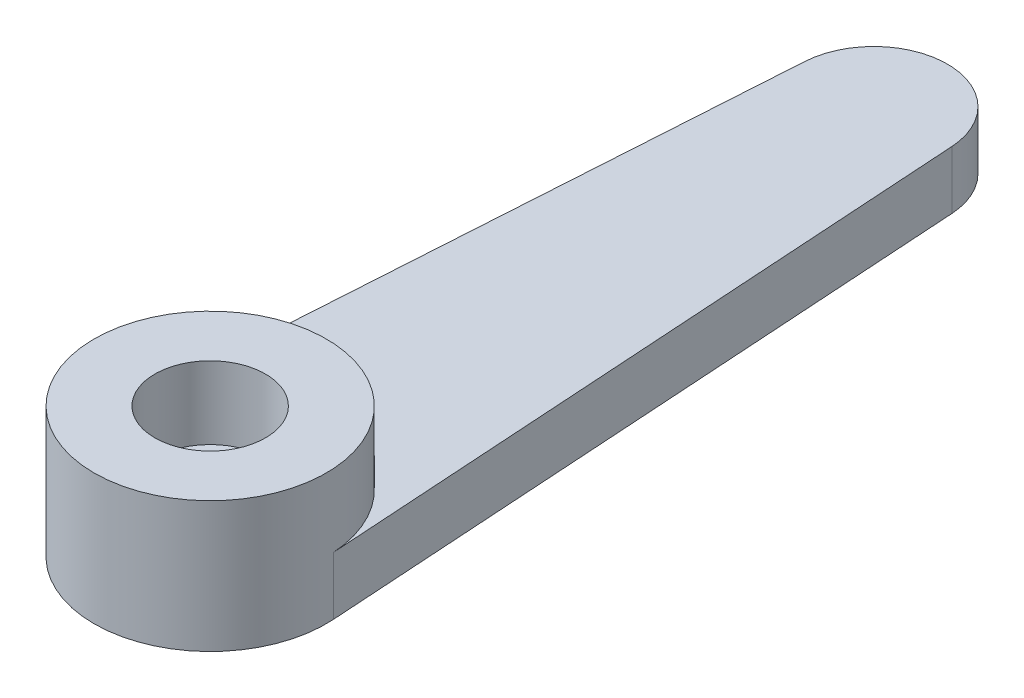
SolidWorks part; units mm, degrees
ref_plane "Front Plane" through (0, 0, 0) normal (0, 0, 1) x (1, 0, 0)
ref_plane "Top Plane" through (0, 0, 0) normal (0, 1, 0) x (1, 0, 0)
ref_plane "Right Plane" through (0, 0, 0) normal (1, 0, 0) x (0, 0, -1)
sketch "Sketch1" plane through (0, 0, 0) normal (0, 1, 0) x (1, 0, 0)
  line L0 (0, 0) -> (0, 25.4) construction
  line L1 (-2.5348, 23.0222) -> (-3.9918, 0.2555)
  line L2 (2.5348, 23.0222) -> (3.9918, 0.2555)
  circle A0 centre (0, 0) radius 4
  circle A1 centre (0, 22.86) radius 2.54
  dimension "D1" = 8
  dimension "D3" = 5.08
  dimension "D2" = 25.4
extrude "Boss-Extrude1" add sketch "Sketch1" along normal blind 2
sketch "Sketch2" plane through (0, 2, 0) normal (0, 1, 0) x (1, 0, 0)
  circle A0 centre (0, 0) radius 4
  circle A1 centre (0, 0) radius 1.9064
extrude "Boss-Extrude2" add sketch "Sketch2" along normal blind 2.5
sketch "Sketch3" plane through (0, 0, 0) normal (0, -1, 0) x (1, 0, 0)
  line L0 (0, 0) -> (0, -25.4) construction
  arc A0 (-2.5348, -23.0222) -> (2.5348, -23.0222) centre (0, -22.86) ccw construction
